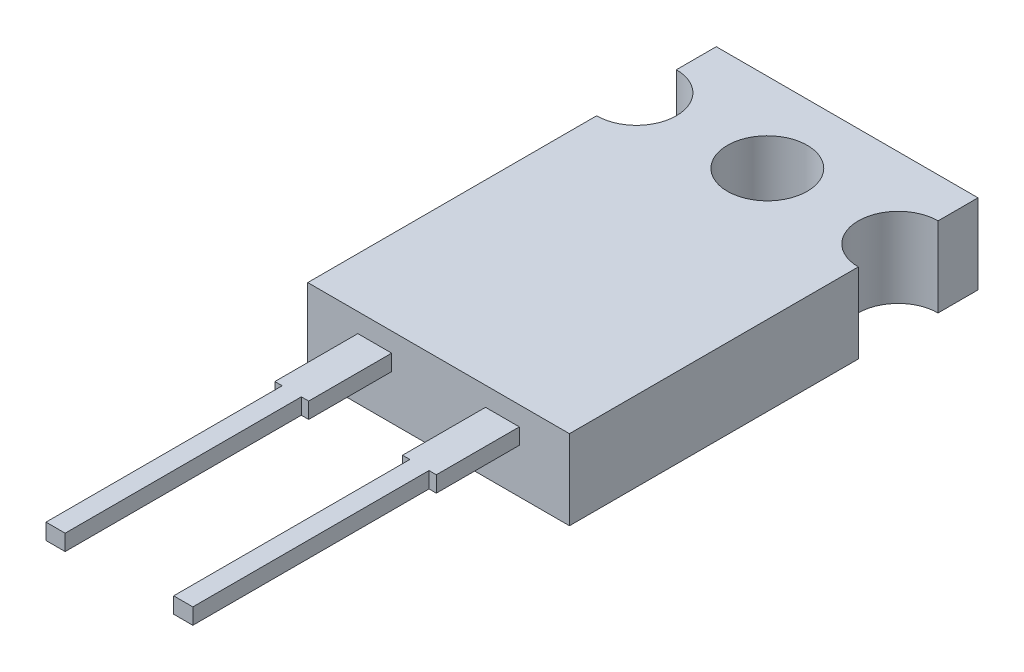
SolidWorks part; units mm, degrees
ref_plane "Front Plane" through (0, 0, 0) normal (0, 0, 1) x (1, 0, 0)
ref_plane "Top Plane" through (0, 0, 0) normal (0, 1, 0) x (1, 0, 0)
ref_plane "Right Plane" through (0, 0, 0) normal (1, 0, 0) x (0, 0, -1)
sketch "Sketch1" plane through (0, 0, 0) normal (0, 1, 0) x (1, 0, 0)
  line L1 (0, 0) -> (10.414, 0)
  line L2 (0, 0) -> (0, 16.256)
  line L3 (0, 16.256) -> (10.414, 16.256)
  line L4 (10.414, 0) -> (10.414, 16.256)
  dimension "D1" = 10.414
  dimension "D2" = 16.256
extrude "Boss-Extrude1" add sketch "Sketch1" along normal blind 3.175 contours L2 L3 L4 L1
sketch "Sketch2" plane through (0, 3.175, 0) normal (0, 1, 0) x (1, 0, 0)
  line L0 (0, 13.081) -> (10.414, 13.081) construction
  line L1 (0, 0) -> (0, 16.256) construction
  line L2 (10.414, 0) -> (10.414, 16.256) construction
  line L3 (0, 16.256) -> (10.414, 16.256) construction
  circle A0 centre (5.207, 13.081) radius 1.5875
  circle A1 centre (10.414, 13.081) radius 1.5875
  circle A2 centre (0, 13.081) radius 1.5875
  dimension "D2" = 3.175
  dimension "D1" = 3.175
extrude "Cut-Extrude1" cut sketch "Sketch2" against normal blind 3.175
sketch "Sketch3" plane through (0, 0, 0) normal (0, 0, 1) x (1, 0, 0)
  line L0 (0, 0) -> (10.414, 0) construction
  line L1 (8.4201, 1.778) -> (7.0739, 1.778)
  line L2 (8.4201, 1.778) -> (8.4201, 2.413)
  line L3 (8.4201, 2.413) -> (7.0739, 2.413)
  line L4 (7.0739, 1.778) -> (7.0739, 2.413)
  line L5 (3.3401, 1.778) -> (1.9939, 1.778)
  line L6 (3.3401, 1.778) -> (3.3401, 2.413)
  line L7 (3.3401, 2.413) -> (1.9939, 2.413)
  line L8 (1.9939, 1.778) -> (1.9939, 2.413)
  line L9 (2.667, 2.413) -> (2.667, 1.778) construction
  line L10 (7.747, 2.413) -> (7.747, 1.778) construction
  line L11 (5.207, 0) -> (5.207, 3.175) construction
  line L12 (0, 3.175) -> (10.414, 3.175) construction
  line L13 (2.667, 2.0955) -> (7.747, 2.0955) construction
  point P20 (5.207, 2.0955)
  point P21 (5.207, 2.0955)
  dimension "D1" = 1.778
  dimension "D2" = 0.635
  dimension "D3" = 1.3462
  dimension "D4" = 5.08
extrude "Boss-Extrude2" add sketch "Sketch3" along normal blind 12.7
sketch "Sketch4" plane through (0, 2.413, 0) normal (0, 1, 0) x (1, 0, 0)
  line L0 (3.3401, -12.7) -> (3.3401, 0) construction
  line L1 (1.9939, -12.7) -> (2.286, -12.7)
  line L2 (1.9939, -12.7) -> (1.9939, -3.302)
  line L3 (1.9939, -3.302) -> (2.286, -3.302)
  line L4 (2.286, -12.7) -> (2.286, -3.302)
  line L5 (3.3401, -12.7) -> (3.048, -12.7)
  line L6 (3.3401, -12.7) -> (3.3401, -3.302)
  line L7 (3.3401, -3.302) -> (3.048, -3.302)
  line L8 (3.048, -12.7) -> (3.048, -3.302)
  line L9 (3.3401, -12.7) -> (1.9939, -12.7) construction
  line L10 (3.3401, 0) -> (1.9939, 0) construction
  line L11 (7.0739, -12.7) -> (7.366, -12.7)
  line L12 (7.0739, -12.7) -> (7.0739, -3.302)
  line L13 (7.0739, -3.302) -> (7.366, -3.302)
  line L14 (7.366, -12.7) -> (7.366, -3.302)
  line L15 (8.4201, -12.7) -> (8.128, -12.7)
  line L16 (8.4201, -12.7) -> (8.4201, -3.302)
  line L17 (8.4201, -3.302) -> (8.128, -3.302)
  line L18 (8.128, -12.7) -> (8.128, -3.302)
  point P23 (0, 0)
  dimension "D1" = 3.302
  dimension "D2" = 0.762
extrude "Cut-Extrude2" cut sketch "Sketch4" against normal through all
